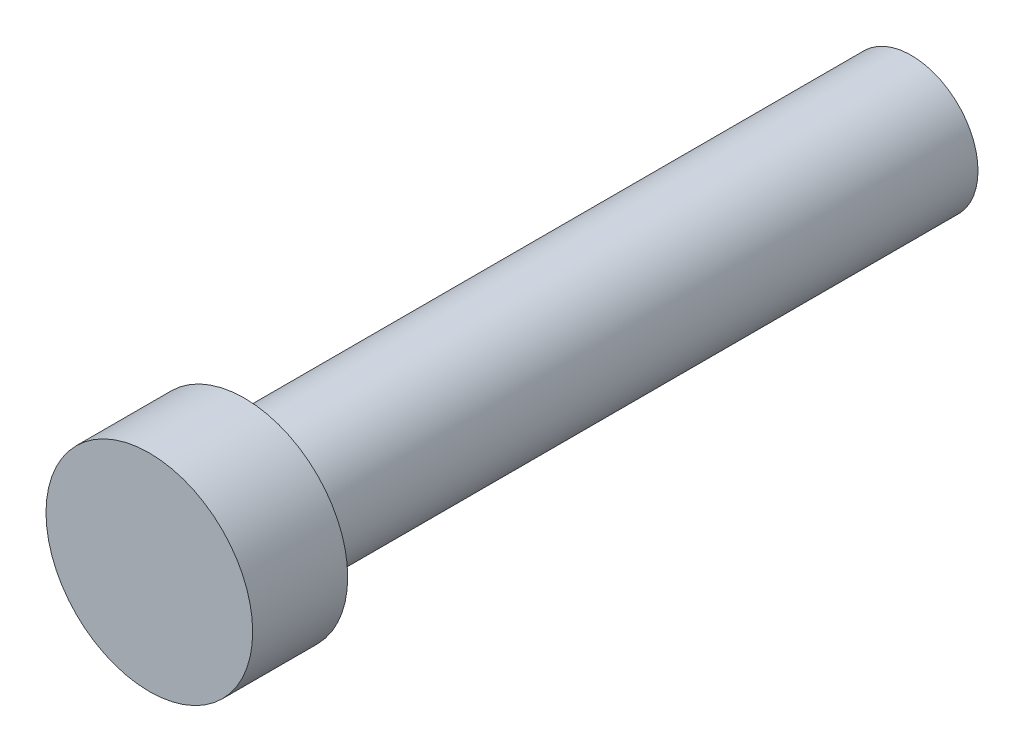
SolidWorks part; units mm, degrees
ref_plane "Front Plane" through (0, 0, 0) normal (0, 0, 1) x (1, 0, 0)
ref_plane "Top Plane" through (0, 0, 0) normal (0, 1, 0) x (1, 0, 0)
ref_plane "Right Plane" through (0, 0, 0) normal (1, 0, 0) x (0, 0, -1)
sketch "Sketch1" plane through (0, 0, 0) normal (0, 0, 1) x (1, 0, 0)
  circle A0 centre (0, 0) radius 4
  dimension "D1" = 8
extrude "Boss-Extrude1" add sketch "Sketch1" along normal blind 40 contours A0
sketch "Sketch2" plane through (0, 0, 40) normal (0, 0, 1) x (1, 0, 0)
  circle A0 centre (0, 0) radius 6.1976
  dimension "D1" = 12.3952
extrude "Boss-Extrude2" add sketch "Sketch2" along normal blind 5.7 contours A0
